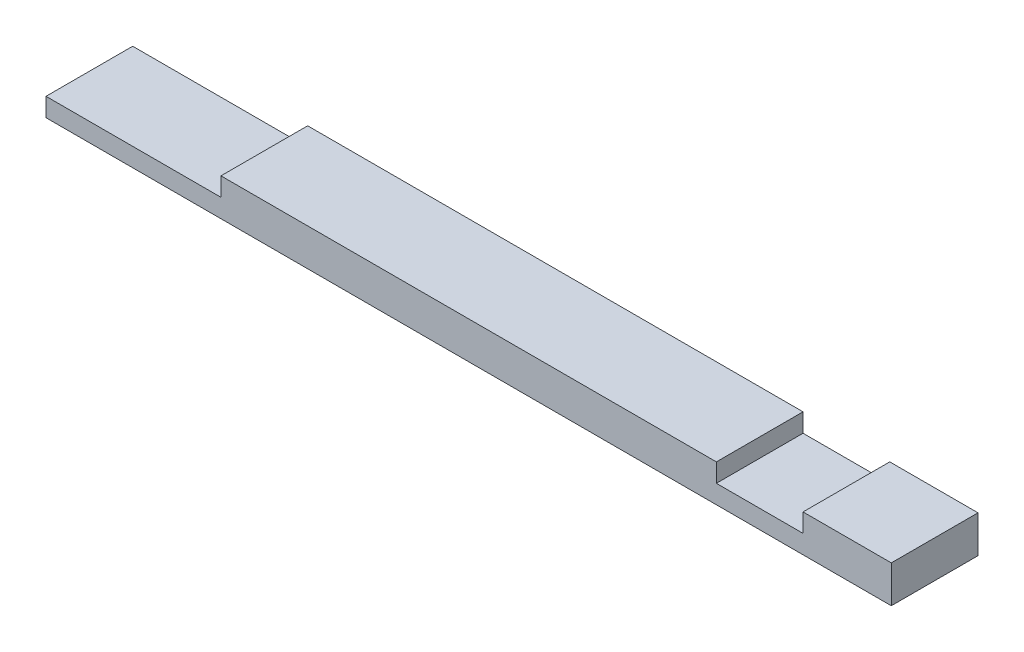
SolidWorks part; units mm, degrees
material "Pine"
ref_plane "Front Plane" through (0, 0, 0) normal (0, 0, 1) x (1, 0, 0)
ref_plane "Top Plane" through (0, 0, 0) normal (0, 1, 0) x (1, 0, 0)
ref_plane "Right Plane" through (0, 0, 0) normal (1, 0, 0) x (0, 0, -1)
sketch "Sketch1" plane through (0, 0, 0) normal (0, 1, 0) x (1, 0, 0)
  line L1 (0, 0) -> (866.775, 0)
  line L2 (0, 0) -> (0, 88.9)
  line L3 (0, 88.9) -> (866.775, 88.9)
  line L4 (866.775, 0) -> (866.775, 88.9)
  dimension "D1" = 88.9
  dimension "D2" = 866.775
extrude "Boss-Extrude1" add sketch "Sketch1" along normal blind 38.1
sketch "Sketch2" plane through (0, 38.1, 0) normal (0, 1, 0) x (1, 0, 0)
  line L0 (866.775, 88.9) -> (0, 88.9) construction
  line L1 (776.2875, 0) -> (687.3875, 0)
  line L2 (776.2875, 0) -> (776.2875, 88.9)
  line L3 (776.2875, 88.9) -> (687.3875, 88.9)
  line L4 (687.3875, 0) -> (687.3875, 88.9)
  line L5 (0, 0) -> (866.775, 0) construction
  line L6 (179.4002, 0) -> (0, 0)
  line L7 (179.4002, 0) -> (179.4002, 88.9)
  line L8 (179.4002, 88.9) -> (0, 88.9)
  line L9 (0, 0) -> (0, 88.9)
  line L13 (0, 88.9) -> (0, 0) construction
  point P15 (776.2875, 44.45)
  dimension "D1" = 179.4002
  dimension "D2" = 88.9
  dimension "D4" = 687.3875
extrude "Cut-Extrude1" cut sketch "Sketch2" against normal blind 19.05
